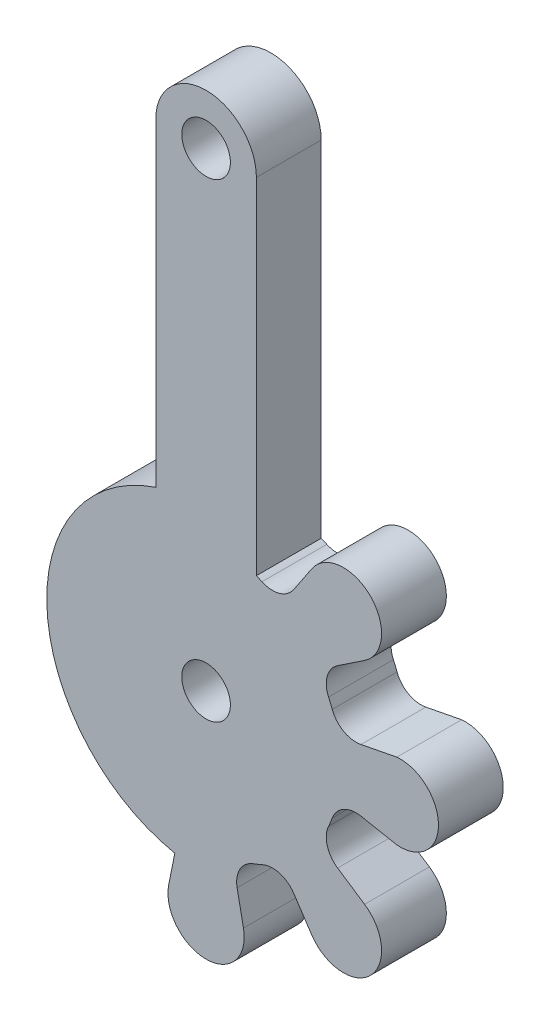
SolidWorks part; units mm, degrees
material "Beech"
ref_plane "Front Plane" through (0, 0, 0) normal (0, 0, 1) x (1, 0, 0)
ref_plane "Top Plane" through (0, 0, 0) normal (0, 1, 0) x (1, 0, 0)
ref_plane "Right Plane" through (0, 0, 0) normal (1, 0, 0) x (0, 0, -1)
sketch "Sketch1" plane through (0, 0, 0) normal (0, 0, 1) x (1, 0, 0)
  line L0 (15.2381, 6.1983) -> (16.3476, 4.5332)
  line L1 (12.1374, 2.7893) -> (11.7446, 4.7512)
  line L2 (7.8987, 4.6746) -> (7.5212, 2.7893)
  line L3 (16.3476, 24.0982) -> (15.2381, 22.4331)
  line L4 (17.9467, 19.7245) -> (19.6118, 20.834)
  line L5 (21.6018, 16.6597) -> (19.3938, 16.231)
  line L6 (19.3938, 12.4004) -> (21.6018, 11.9717)
  line L7 (19.6118, 7.7974) -> (17.9467, 8.9069)
  line L8 (12.9343, 43.3157) -> (12.9343, 22.0244)
  line L9 (6.7243, 43.3157) -> (6.7243, 23.6451)
  arc A0 (15.2381, 6.1983) -> (13.2805, 6.7557) centre (13.9322, 5.3281) ccw
  arc A1 (12.7347, 6.5296) -> (13.2805, 6.7557) centre (9.8293, 14.3157) ccw
  arc A2 (12.7347, 6.5296) -> (11.7446, 4.7512) centre (13.2833, 5.0593) ccw
  arc A3 (12.1703, 2.5732) -> (12.1374, 2.7893) centre (9.8293, 2.3271) ccw
  arc A4 (7.5212, 2.7893) -> (7.4882, 2.5732) centre (9.8293, 2.3271) ccw
  arc A5 (13.2805, 21.8757) -> (12.9343, 22.0244) centre (9.8293, 14.3157) ccw
  arc A6 (13.2805, 21.8757) -> (15.2381, 22.4331) centre (13.9322, 23.3033) ccw
  arc A7 (16.4771, 24.2743) -> (16.3476, 24.0982) centre (18.3065, 22.7929) ccw
  arc A8 (19.6118, 20.834) -> (19.7879, 20.9635) centre (18.3065, 22.7929) ccw
  arc A9 (17.9467, 19.7245) -> (17.3893, 17.7669) centre (18.8169, 18.4186) ccw
  arc A10 (17.6154, 17.2211) -> (17.3893, 17.7669) centre (9.8293, 14.3157) ccw
  arc A11 (17.6154, 17.2211) -> (19.3938, 16.231) centre (19.0857, 17.7697) ccw
  arc A12 (19.3938, 12.4004) -> (17.6154, 11.4103) centre (19.0857, 10.8617) ccw
  arc A13 (17.3893, 10.8645) -> (17.6154, 11.4103) centre (9.8293, 14.3157) ccw
  arc A14 (17.3893, 10.8645) -> (17.9467, 8.9069) centre (18.8169, 10.2128) ccw
  arc A15 (19.7879, 7.6679) -> (19.6118, 7.7974) centre (18.3065, 5.8385) ccw
  arc A16 (16.3476, 4.5332) -> (16.4771, 4.3571) centre (18.3065, 5.8385) ccw
  arc A17 (7.4853, 2.5432) -> (12.1733, 2.5432) centre (9.8293, 2.3271) ccw
  arc A18 (21.6018, 11.9717) -> (21.6018, 16.6597) centre (21.8179, 14.3157) ccw
  arc A19 (19.8112, 20.9826) -> (16.4962, 24.2976) centre (18.3065, 22.7929) ccw
  arc A20 (16.4962, 4.3338) -> (19.8112, 7.6488) centre (18.3065, 5.8385) ccw
  arc A21 (19.7879, 20.9635) -> (19.8112, 20.9826) centre (18.3065, 22.7929) ccw
  arc A22 (16.4962, 24.2976) -> (16.4771, 24.2743) centre (18.3065, 22.7929) ccw
  arc A23 (7.4882, 2.5732) -> (7.4853, 2.5432) centre (9.8293, 2.3271) ccw
  arc A24 (12.1733, 2.5432) -> (12.1703, 2.5732) centre (9.8293, 2.3271) ccw
  arc A25 (16.4771, 4.3571) -> (16.4962, 4.3338) centre (18.3065, 5.8385) ccw
  arc A26 (19.8112, 7.6488) -> (19.7879, 7.6679) centre (18.3065, 5.8385) ccw
  arc A27 (6.7243, 23.6451) -> (7.8987, 4.6746) centre (9.8293, 14.3157) ccw
  circle A28 centre (9.8293, 14.3157) radius 1.5
  circle A29 centre (9.8293, 43.3157) radius 1.5
  arc A30 (12.9343, 43.3157) -> (6.7243, 43.3157) centre (9.8293, 43.3157) ccw
extrude "Boss-Extrude1" add sketch "Sketch1" along normal blind 4
